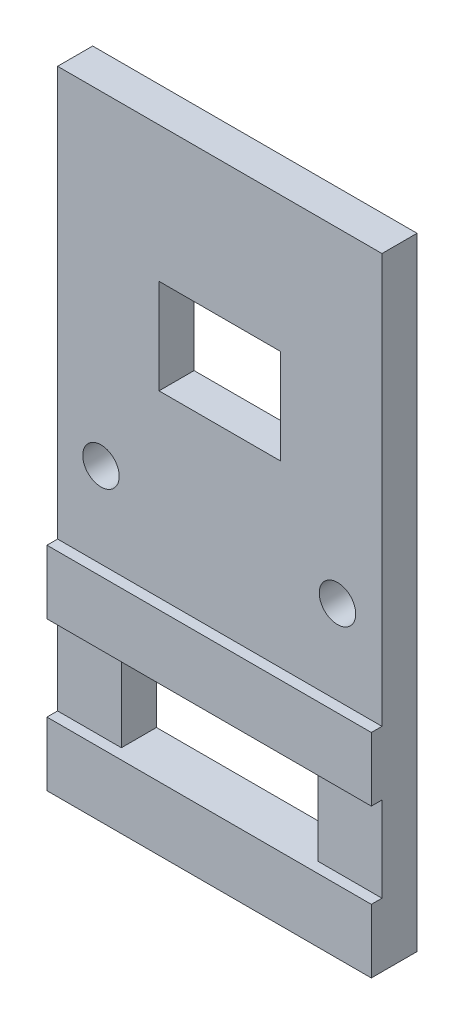
SolidWorks part; units mm, degrees
ref_plane "前基準面" through (0, 0, 0) normal (0, 0, 1) x (1, 0, 0)
ref_plane "上基準面" through (0, 0, 0) normal (0, 1, 0) x (1, 0, 0)
ref_plane "右基準面" through (0, 0, 0) normal (1, 0, 0) x (0, 0, -1)
sketch "草圖1" plane through (0, 0, 0) normal (0, 0, 1) x (1, 0, 0)
  line L0 (15.254, 40.6772) -> (-15.254, 40.6772)
  line L1 (-15.254, 40.6772) -> (-15.254, -17.8338)
  line L2 (15.254, 40.6772) -> (15.254, -17.8338)
  line L4 (-5.7123, 27.9319) -> (5.7123, 27.9319)
  line L5 (-5.7123, 27.9319) -> (-5.7123, 19.0094)
  line L6 (-5.7123, 19.0094) -> (5.7123, 19.0094)
  line L7 (5.7123, 27.9319) -> (5.7123, 19.0094)
  line L9 (-15.254, 2.1662) -> (15.254, 2.1662)
  line L10 (-15.254, 2.1662) -> (-15.254, -3.8338)
  line L11 (-15.254, -3.8338) -> (15.254, -3.8338)
  line L12 (15.254, 2.1662) -> (15.254, -3.8338)
  line L13 (-15.254, -11.8338) -> (15.254, -11.8338)
  line L14 (-15.254, -11.8338) -> (-15.254, -17.8338)
  line L15 (-15.254, -17.8338) -> (15.254, -17.8338)
  line L16 (15.254, -11.8338) -> (15.254, -17.8338)
  line L17 (-15.254, 40.6772) -> (15.254, 40.6772)
  line L18 (-15.254, 40.6772) -> (-15.254, -17.8338)
  line L19 (-15.254, -17.8338) -> (15.254, -17.8338)
  line L20 (15.254, 40.6772) -> (15.254, -17.8338)
  circle A0 centre (-11.1744, 10.1662) radius 1.7161
  circle A1 centre (11.0708, 10.0808) radius 1.7161
  dimension "D1" = 6
  dimension "D3" = 8
  dimension "D4" = 8
  dimension "D5" = 6
extrude "填料-伸長1" add sketch "草圖1" along normal blind 3.3 contours L7 L4 L5 L6 | L18 L17 L20 L19 | A1 | A0
sketch "草圖2" plane through (0, 0, 3.3) normal (0, 0, 1) x (1, 0, 0)
  line L8 (-15.254, -17.8338) -> (15.254, -17.8338) construction
  line L9 (-15.254, 2.1662) -> (15.254, 2.1662)
  line L11 (-15.254, -3.8338) -> (15.254, -3.8338)
  line L12 (15.254, 2.1662) -> (15.254, -3.8338)
  line L13 (-15.254, -11.8338) -> (15.254, -11.8338)
  line L15 (-15.254, -17.8338) -> (15.254, -17.8338)
  line L16 (15.254, -11.8338) -> (15.254, -17.8338)
  line L17 (15.254, 40.6772) -> (15.254, -17.8338) construction
  line L20 (-15.254, -17.8338) -> (-15.254, 2.1662)
  line L21 (-15.254, 40.6772) -> (-15.254, -17.8338) construction
  line L23 (-15.254, 2.1662) -> (15.254, 2.1662)
  line L24 (-15.254, 2.1662) -> (-15.254, -3.8338)
  line L25 (-15.254, -3.8338) -> (15.254, -3.8338)
  line L26 (15.254, 2.1662) -> (15.254, -3.8338)
  line L27 (-15.254, -11.8338) -> (15.254, -11.8338)
  line L28 (-15.254, -11.8338) -> (-15.254, -17.8338)
  line L29 (-15.254, -17.8338) -> (15.254, -17.8338)
  line L30 (15.254, -11.8338) -> (15.254, -17.8338)
  line M27 (-15.254, -17.8338) -> (15.254, -17.8338)
  line M28 (15.254, -17.8338) -> (15.254, 40.6772)
  line M30 (-15.254, 40.6772) -> (-15.254, -17.8338)
extrude "填料-伸長2" add sketch "草圖2" along normal blind 1 contours L11 L9 M30 M28 | L13 M30 M27 M28
sketch "草圖3" plane through (0, 0, 3.3) normal (0, 0, 1) x (1, 0, 0)
  line L0 (-15.254, -3.8338) -> (15.254, -3.8338) construction
  line L1 (-9.254, -3.8338) -> (9.254, -3.8338)
  line L2 (-9.254, -3.8338) -> (-9.254, -11.8338)
  line L3 (-9.254, -11.8338) -> (9.254, -11.8338)
  line L4 (9.254, -3.8338) -> (9.254, -11.8338)
  line L5 (-15.254, -11.8338) -> (15.254, -11.8338) construction
  line L6 (-15.254, -3.8338) -> (-15.254, -11.8338) construction
  line L7 (15.254, -3.8338) -> (15.254, -11.8338) construction
  dimension "D1" = 6
  dimension "D2" = 6
extrude "除料-伸長1" cut sketch "草圖3" against normal blind 3.3 contours L2 L1 L4 L3
